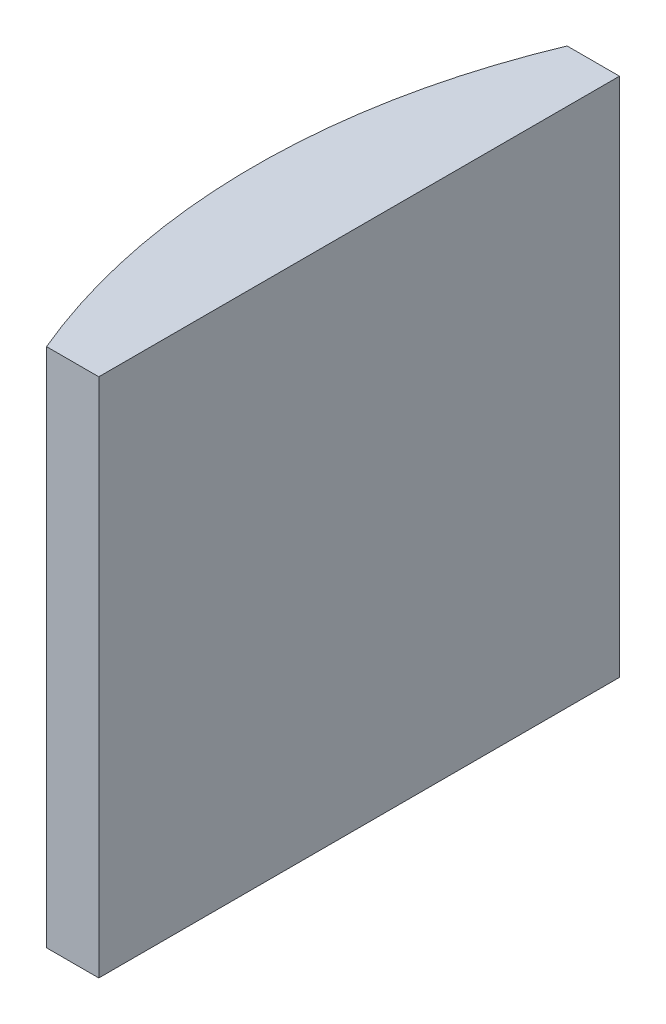
SolidWorks part; units mm, degrees
ref_plane "前视基准面" through (0, 0, 0) normal (0, 0, 1) x (1, 0, 0)
ref_plane "上视基准面" through (0, 0, 0) normal (0, 1, 0) x (1, 0, 0)
ref_plane "右视基准面" through (0, 0, 0) normal (1, 0, 0) x (0, 0, -1)
sketch "草图1" plane through (0, 0, 0) normal (0, 1, 0) x (1, 0, 0)
  line L0 (10.7432, 0) -> (-19.1624, 0) construction
  line L1 (-19.4822, 10) -> (-17.4748, 10)
  line L2 (-19.4822, -10) -> (-17.4748, -10)
  line L3 (-17.4748, 10) -> (-17.4748, -10)
  arc A0 (-19.4822, 10) -> (-19.4822, -10) centre (4.3552, 0) ccw
  point P19 (-21.4948, 0)
  point P20 (-17.4748, 0)
  dimension "D2" = 10
  dimension "D3" = 25.85
  dimension "D4" = 4.02
  dimension "D1" = 10
extrude "凸台-拉伸1" add sketch "草图1" along normal blind 20
